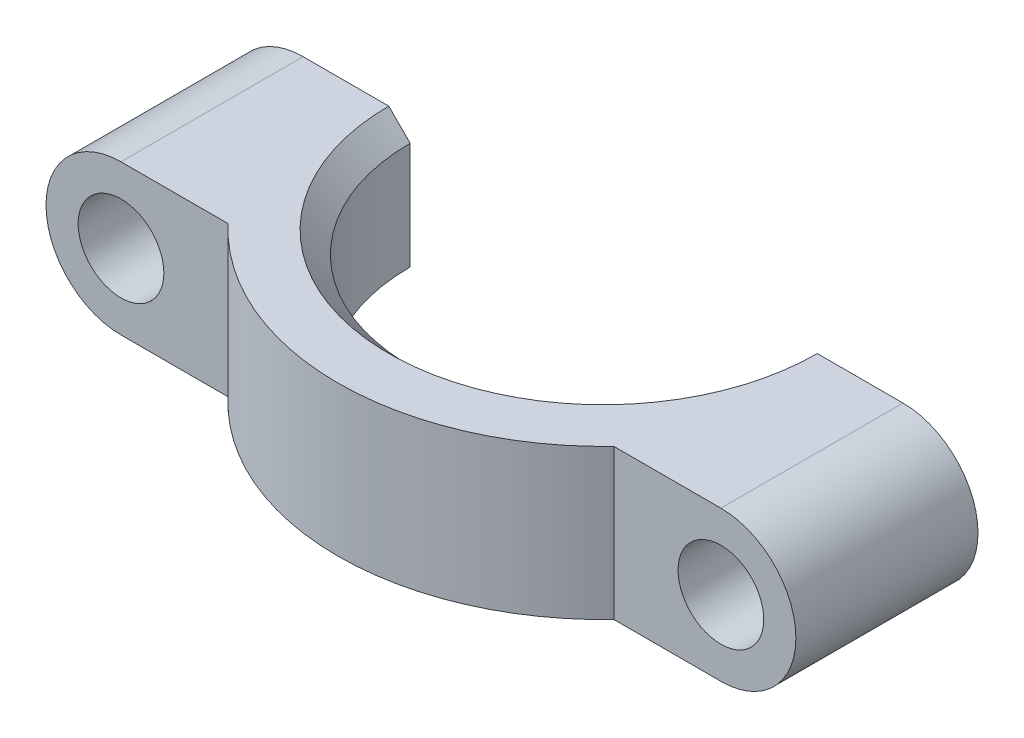
SolidWorks part; units mm, degrees
ref_plane "Planta" through (0, 0, 0) normal (0, 0, 1) x (1, 0, 0)
ref_plane "Alzado" through (0, 0, 0) normal (0, 1, 0) x (1, 0, 0)
ref_plane "Vista lateral" through (0, 0, 0) normal (1, 0, 0) x (0, 0, -1)
sketch "Croquis1" plane through (0, 0, 0) normal (0, 0, 1) x (1, 0, 0)
  line L0 (5, 0) -> (23, 0)
  line L1 (31.5, 0) -> (28, 0)
  line L3 (5, 0) -> (5, 3.5)
  line L4 (5, 3.5) -> (0, 3.5)
  line L5 (5, 0) -> (5, -3.5)
  line L6 (5, -3.5) -> (0, -3.5)
  line L7 (31.5, 0) -> (28, 0)
  line L8 (23, 0) -> (23, 3.5)
  line L9 (23, 3.5) -> (28, 3.5)
  line L10 (23, 0) -> (23, -3.5)
  line L11 (23, -3.5) -> (28, -3.5)
  line L12 (28, 0) -> (31.5, 0)
  arc A0 (0, 3.5) -> (0, -3.5) centre (0, 0) ccw
  arc A1 (28, -3.5) -> (28, 3.5) centre (28, 0) ccw
  circle A2 centre (0, 0) radius 2
  circle A3 centre (28, 0) radius 2
  dimension "D1" = 7
  dimension "D2" = 4
  dimension "D4" = 4
  dimension "D3" = 3.5
  dimension "D5" = 8.5
extrude "Saliente-Extruir1" add sketch "Croquis1" along normal blind 8.5
sketch "Croquis2" plane through (0, -3.5, 0) normal (0, -1, 0) x (1, 0, 0)
  line L0 (1.6206, 0) -> (5, 0)
  line L1 (23, 0) -> (26.3794, 0)
  arc A0 (23, 0) -> (5, 0) centre (14, 0) ccw
  arc A1 (26.3794, 0) -> (1.6206, 0) centre (14, 0) ccw
  dimension "D1" = 12.3794
extrude "Saliente-Extruir2" add sketch "Croquis2" against normal through all
chamfer "Chaflán1" distance 1 angle 45 2 edges at (14, -3.5, 9) (14, 3.5, 9)
